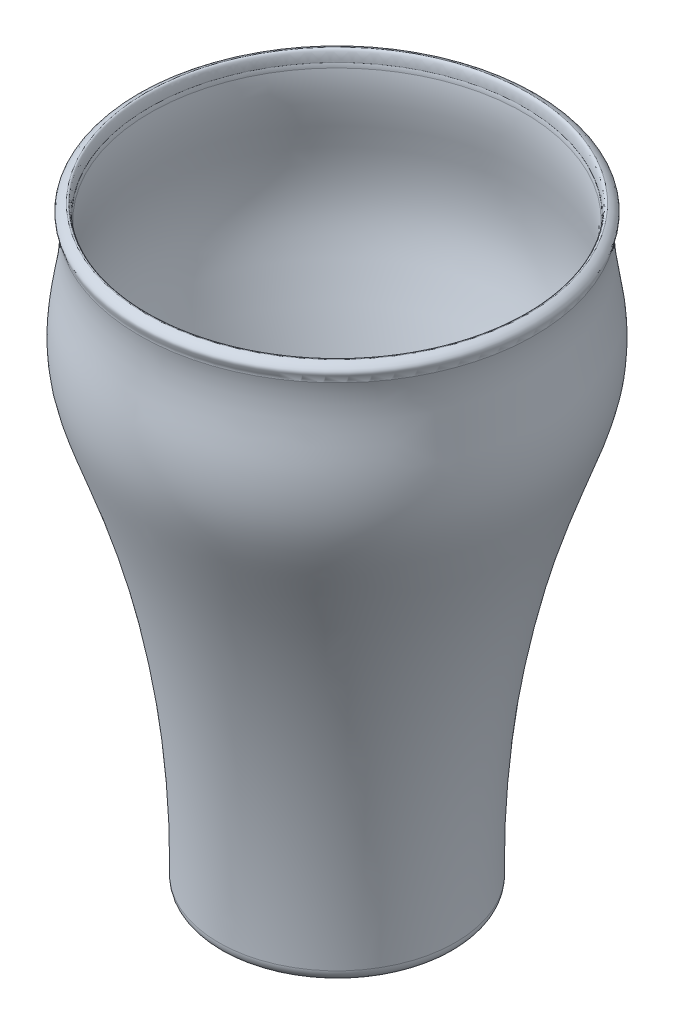
SolidWorks part; units mm, degrees
ref_plane "Front" through (0, 0, 0) normal (0, 0, 1) x (1, 0, 0)
ref_plane "Top" through (0, 0, 0) normal (0, 1, 0) x (1, 0, 0)
ref_plane "Right" through (0, 0, 0) normal (1, 0, 0) x (0, 0, -1)
sketch "Sketch2" plane through (0, 0, 0) normal (0, 0, 1) x (1, 0, 0)
  line L1 (0, 70.0373) -> (0, -56.9627) construction
  line L3 (-40.9828, 70.0373) -> (0, 70.0373) construction
  line L4 (-25.4071, -56.9627) -> (0, -56.9627)
  line L5 (0, 70.0373) -> (40.9828, 70.0373) construction
  line L6 (0, -56.9627) -> (25.4071, -56.9627) construction
  line L7 (-23.0968, -54.6894) -> (-2.2733, -54.6894)
  line L10 (-40.1617, 67.764) -> (-2.2733, 67.764) construction
  line L11 (-2.2733, 67.764) -> (-2.2733, -54.6894) construction
  line L12 (-2.2733, -54.6894) -> (0, -54.6894)
  line L13 (0, -54.6894) -> (0, -56.9627)
  spline S0 degree 3 poles (-40.9828, 70.0373) (-41.2541, 69.951) (-42.0561, 69.5973) (-43.2006, 68.443) (-42.2333, 67.3091) (-42.2865, 66.6426) knots 0 0 0 0 0.262567 0.525657 1 1 1 1
  spline S1 degree 3 poles (-42.2865, 66.6426) (-41.7851, 63.8343) (-42.2065, 58.4269) (-43.9755, 49.6279) (-44.1381, 39.0617) (-40.0103, 27.5218) (-28.8073, -3.4178) (-24.8923, -32.5522) (-25.4071, -56.9627) knots 0 0 0 0 0.067526 0.127886 0.214327 0.314757 0.416925 1 1 1 1
  spline S2 degree 3 poles (42.2865, 66.6426) (41.7851, 63.8343) (42.2065, 58.4269) (43.9755, 49.6279) (44.1381, 39.0617) (40.0103, 27.5218) (28.8073, -3.4178) (24.8923, -32.5522) (25.4071, -56.9627) knots 0 0 0 0 0.067526 0.127886 0.214327 0.314757 0.416925 1 1 1 1 construction
  spline S3 degree 3 poles (40.9828, 70.0373) (41.2541, 69.951) (42.0561, 69.5973) (43.2006, 68.443) (42.2333, 67.3091) (42.2865, 66.6426) knots 0 0 0 0 0.262567 0.525657 1 1 1 1 construction
  spline S4 degree 1 poles (-40.0115, 66.8275) (-23.0968, -54.6894) knots 0 0 1 1 construction
  spline S5 degree 1 poles (-40.1617, 67.764) (-40.0115, 66.8275) knots 0 0 1 1 construction
  spline S6 degree 3 poles (-40.0115, 66.8275) (-39.8926, 66.1154) (-39.7343, 64.6647) (-39.6956, 61.8473) (-40.1657, 57.0559) (-41.1878, 52.0481) (-41.6499, 47.1721) (-41.6727, 43.4965) (-41.325, 39.9175) (-40.3025, 35.2101) (-38.2199, 29.2319) (-35.5578, 21.9302) (-33.0638, 14.5721) (-30.1181, 4.5933) (-27.1385, -8.0821) (-24.664, -23.5305) (-23.2671, -39.1117) (-23.0388, -49.4956) (-23.0968, -54.6894) knots 0.001517 0.001517 0.001517 0.001517 0.016833 0.032148 0.062779 0.124041 0.154672 0.185303 0.215934 0.246564 0.307826 0.369088 0.43035 0.491612 0.614135 0.736659 0.859182 0.981706 0.981706 0.981706 0.981706
  spline S7 degree 3 poles (-40.1617, 67.764) (-40.1432, 67.6985) (-40.1102, 67.5721) (-40.0635, 67.3488) (-40.0278, 67.1058) (-40.0142, 66.9183) (-40.0115, 66.8275) knots 0.882607 0.882607 0.882607 0.882607 0.905087 0.927568 0.950048 0.972528 0.972528 0.972528 0.972528
  spline S8 degree 3 poles (-40.1617, 67.764) (-40.2079, 67.5717) (-40.1071, 70.3158) (-40.9828, 70.0373) knots 0 0 0 0 1 1 1 1
  dimension "D1" = 127
  dimension "D2" = 84.7336
  dimension "D3" = 2.2733
revolve "Revolve1" add sketch "Sketch2" angle 360 about L1
fillet "Fillet1" radius 2.54 1 edges at (0, -54.6894, 23.0968)
fillet "Fillet2" radius 2.54 1 edges at (0, -56.9627, 25.4071)
